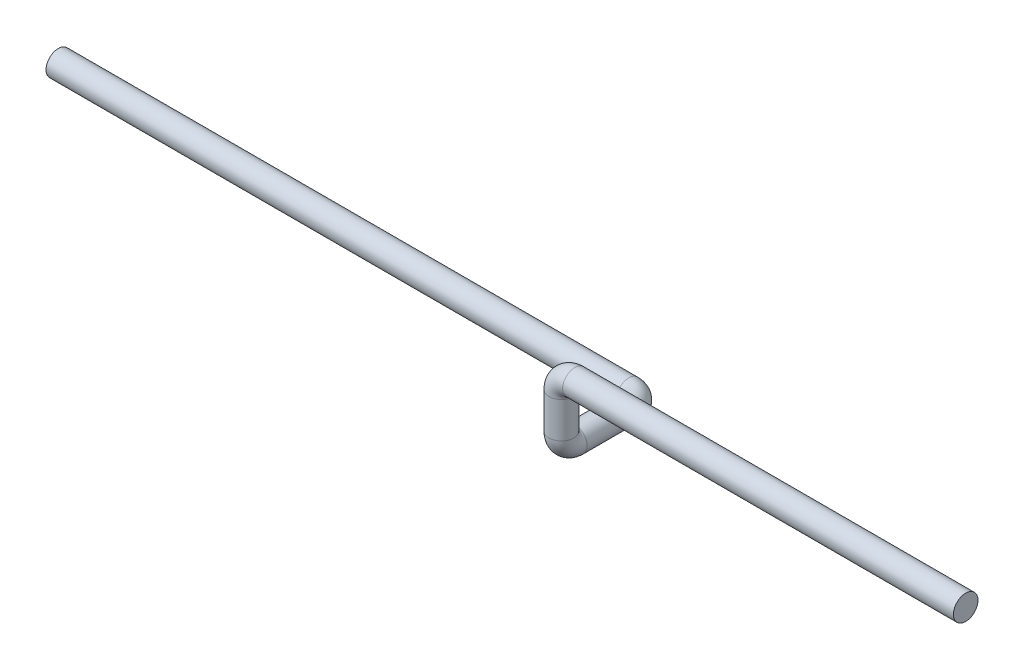
SolidWorks part; units mm, degrees
ref_plane "Alzado" through (0, 0, 0) normal (0, 0, 1) x (1, 0, 0)
ref_plane "Planta" through (0, 0, 0) normal (0, 1, 0) x (1, 0, 0)
ref_plane "Vista lateral" through (0, 0, 0) normal (1, 0, 0) x (0, 0, -1)
sketch3d "Croquis3D1"
  line L0 (0, 0, 0) -> (-435, 0, 0)
  line L1 (-450, -15, 0) -> (-450, -55, 0)
  line L2 (-450, -70, -15) -> (-450, -70, -75)
  line L3 (-465, -70, -90) -> (-1100, -70, -90)
  arc A0 (-435, 0, 0) -> (-450, -15, 0) centre (-435, -15, 0) ccw
  arc A1 (-450, -55, 0) -> (-450, -70, -15) centre (-450, -55, -15) ccw
  arc A2 (-450, -70, -75) -> (-465, -70, -90) centre (-465, -70, -75) ccw
  point P8 (-450, 0, 0)
  point P9 (-435, -15, 15)
  point P12 (-450, -70, 0)
  point P13 (-435, -55, -15)
  point P16 (-450, -70, -90)
  point P17 (-465, -55, -75)
  dimension "D1" = 450
  dimension "D2" = 70
  dimension "D5" = 15
  dimension "D3" = 90
  dimension "D4" = 650
sketch "Croquis1" plane through (0, 0, 0) normal (1, 0, 0) x (0, 0, -1)
  circle A0 centre (0, 0) radius 13.7
  dimension "D1" = 27.4
sweep "Barrer1" add profiles "Croquis1" path "Croquis3D1"
